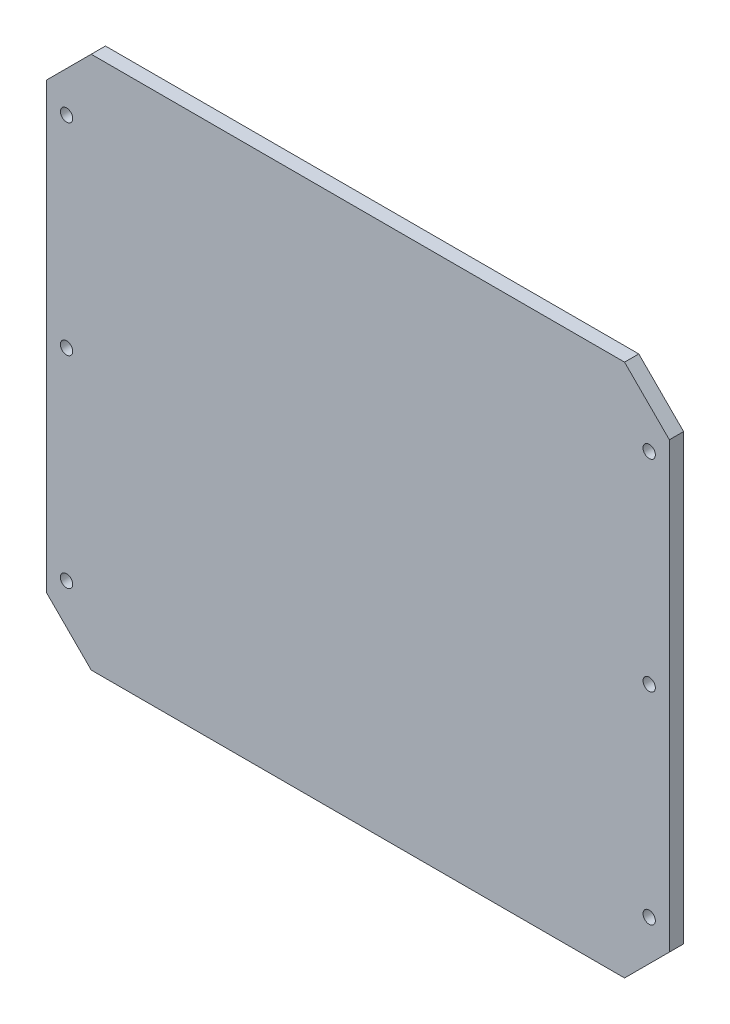
SolidWorks part; units mm, degrees
ref_plane "Front Plane" through (0, 0, 0) normal (0, 0, 1) x (1, 0, 0)
ref_plane "Top Plane" through (0, 0, 0) normal (0, 1, 0) x (1, 0, 0)
ref_plane "Right Plane" through (0, 0, 0) normal (1, 0, 0) x (0, 0, -1)
sketch "Sketch1" plane through (0, 0, 0) normal (0, 0, 1) x (1, 0, 0)
  line L0 (-79.0045, 0) -> (94.053, 0) construction
  line L1 (0, 67.0127) -> (0, -68.6587) construction
  line L3 (139, -119) -> (-139, -119)
  line L4 (139, -119) -> (139, 119)
  line L5 (139, 119) -> (-139, 119)
  line L6 (-139, -119) -> (-139, 119)
  line L7 (139, -119) -> (-139, 119) construction
  line L8 (139, 119) -> (-139, -119) construction
  point P4 (0, 0)
  dimension "D1" = 238
  dimension "D2" = 278
extrude "Boss-Extrude1" add sketch "Sketch1" along normal blind 6.35
chamfer "Chamfer1" distance 20 angle 45 4 edges at (139, -119, 3.175) (139, 119, 3.175) (-139, 119, 3.175) (-139, -119, 3.175)
sketch "Sketch4" plane through (0, 0, 6.35) normal (0, 0, 1) x (1, 0, 0)
  line L0 (0, 186.846) -> (0, -174.5938) construction
  line L1 (219.7737, 0) -> (-232.7917, 0) construction
  line L4 (-139, 99) -> (-139, -99) construction
  circle A6 centre (-130, 90) radius 2.75
  circle A7 centre (-130, -90) radius 2.75
  circle A8 centre (-130, 0) radius 2.75
  circle A9 centre (130, -90) radius 2.75
  circle A10 centre (130, 0) radius 2.75
  circle A11 centre (130, 90) radius 2.75
  dimension "D6" = 5.5
  dimension "D7" = 5.5
  dimension "D4" = 9
  dimension "D5" = 90
extrude "Cut-Extrude2" cut sketch "Sketch4" against normal blind 76.2
equation "\"plate_thickness\" = 6.35 'thickness of the plate "
equation "\"D1@Boss-Extrude1\"=\"plate_thickness\""
equation "\"connector_D1\" = 70 'the big holes diameter"
equation "\"mtg_hole_D\" = 5.5 'mounting holes"
equation "\"mtg_dfc\" = 40 'mounting hole distance from center"
equation "\"t_height\" = 200"
equation "\"t_width\" = 240"
equation "\"t_length\" = 240"
equation "\"plate_hole_from_edge\" = 9"
equation "\"plate_spacing\" = 1"
equation "\"front_plate_height\" = \"t_height\" + 38"
equation "\"front_plate_width\" = \"t_width\" + 38"
equation "\"side_plate_height\" = \"front_plate_height\""
equation "\"side_plate_length\" = \"t_length\" + 38"
equation "\"top_plate_width\" = \"front_plate_width\""
equation "\"top_plate_length\" = \"side_plate_length\""
equation "\"D2@Sketch1\"=\"side_plate_length\""
equation "\"D1@Sketch1\"=\"side_plate_height\""
equation "\"D4@Sketch4\"=\"plate_hole_from_edge\""
equation "\"D6@Sketch4\"=\"mtg_hole_D\""
equation "\"D7@Sketch4\"=\"mtg_hole_D\""
